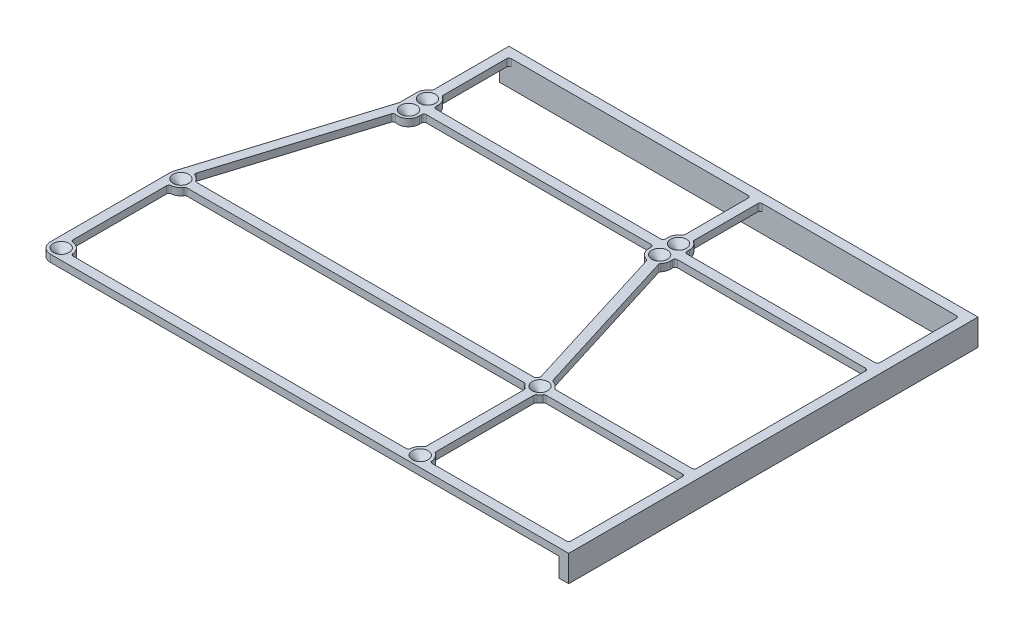
SolidWorks part; units mm, degrees
ref_plane "Front Plane" through (0, 0, 0) normal (0, 0, 1) x (1, 0, 0)
ref_plane "Top Plane" through (0, 0, 0) normal (0, 1, 0) x (1, 0, 0)
ref_plane "Right Plane" through (0, 0, 0) normal (1, 0, 0) x (0, 0, -1)
sketch "Sketch1" plane through (0, 0, 0) normal (0, 1, 0) x (1, 0, 0)
  line L0 (0, 0) -> (-83.045, 0)
  line L1 (-191.955, 0) -> (-191.955, 4)
  line L2 (-191.955, 4) -> (4, 4)
  line L3 (4, 4) -> (4, -167)
  line L4 (4, -167) -> (0, -167)
  line L5 (0, -163) -> (0, -114.5)
  line L6 (-189.955, -32.045) -> (-189.955, -39.955) construction
  line L7 (-245, -80) -> (-30, -80) construction
  line L8 (-245, -80) -> (-245, -195) construction
  line L9 (-245, -195) -> (-30, -195) construction
  line L10 (-30, -80) -> (-30, -195) construction
  line L11 (-212.5, -112.5) -> (-62.5, -112.5) construction
  line L12 (-212.5, -112.5) -> (-212.5, -162.5) construction
  line L13 (-212.5, -162.5) -> (-62.5, -162.5) construction
  line L14 (-62.5, -112.5) -> (-62.5, -162.5) construction
  line L15 (-193.55, -25) -> (-81.45, -25) construction
  line L16 (-193.55, -25) -> (-193.55, -47) construction
  line L17 (-193.55, -47) -> (-81.45, -47) construction
  line L18 (-81.45, -25) -> (-81.45, -47) construction
  line L19 (-189.955, -36) -> (-85.045, -36) construction
  line L20 (-85.045, -32.045) -> (-85.045, -39.955) construction
  line L21 (-194.455, -32.045) -> (-194.455, -39.2719)
  line L22 (-185.455, -32.045) -> (-185.455, -34)
  line L23 (-191.955, 0) -> (-191.955, -28.0139)
  line L24 (-187.955, -28.0139) -> (-187.955, 0)
  line L25 (-191.955, 0) -> (-187.955, 0) construction
  line L26 (-89.545, -32.045) -> (-89.545, -34)
  line L27 (-80.545, -32.045) -> (-80.545, -34)
  line L28 (-87.045, -28.0139) -> (-87.045, 0)
  line L29 (-83.045, -28.0139) -> (-83.045, 0)
  line L30 (-87.045, 0) -> (-187.955, 0)
  line L31 (-87.045, 0) -> (-83.045, 0) construction
  line L32 (-58.4689, -114.5) -> (0, -114.5)
  line L33 (-58.4689, -110.5) -> (0, -110.5)
  line L34 (-60.5, -116.5311) -> (-60.5, -158.4689)
  line L35 (0, -167) -> (-212.5, -167)
  line L36 (-58.0279, -163) -> (0, -163)
  line L37 (0, -163) -> (0, -167) construction
  line L38 (-208.0279, -163) -> (-66.9721, -163)
  line L39 (-64.5, -116.5311) -> (-64.5, -158.4689)
  line L40 (-213, -116.9721) -> (-213, -158.0279)
  line L41 (-208.4689, -114.5) -> (-66.5311, -114.5)
  line L42 (-216.7973, -111.1645) -> (-194.455, -39.2719)
  line L43 (-189.955, -39.955) -> (-212.5, -112.5) construction
  line L44 (-217, -112.5) -> (-217, -162.5)
  line L45 (-58.0279, -163) -> (-62.0031, -162.5556) construction
  line L46 (-191.7597, -44.0773) -> (-211.6503, -108.081)
  line L47 (-208.4689, -110.5) -> (-66.5311, -110.5)
  line L48 (-85.045, -39.955) -> (-62.5, -112.5) construction
  line L49 (-65.6062, -109.244) -> (-85.7586, -44.3981)
  line L50 (-61.7864, -108.0569) -> (-81.9388, -43.211)
  line L51 (-65.6062, -109.244) -> (-61.7864, -108.0569) construction
  line L52 (0, -110.5) -> (0, -38)
  line L53 (0, -110.5) -> (0, -114.5) construction
  line L54 (-64.5, -158.4689) -> (-60.5, -158.4689) construction
  line L55 (-213, -116.9721) -> (-217, -116.9721) construction
  line L56 (-66.5311, -110.5) -> (-66.5311, -114.5) construction
  line L57 (-211.6503, -108.081) -> (-215.4701, -106.8939) construction
  line L58 (-185.455, -34) -> (-89.545, -34)
  line L59 (-185.455, -38) -> (-89.545, -38)
  line L60 (-185.455, -38) -> (-185.455, -39.955)
  line L61 (-89.545, -38) -> (-89.545, -39.955)
  line L62 (-185.455, -34) -> (-185.455, -38) construction
  line L63 (-80.545, -34) -> (0, -34)
  line L64 (-80.545, -38) -> (0, -38)
  line L65 (-80.545, -38) -> (-80.545, -39.955)
  line L66 (0, -34) -> (0, 0)
  arc A0 (-66.9721, -163) -> (-64.5, -158.4689) centre (-62.5, -162.5) cw
  arc A1 (-60.5, -158.4689) -> (-58.0279, -163) centre (-62.5, -162.5) cw
  arc A2 (-212.5, -167) -> (-217, -162.5) centre (-212.5, -162.5) cw
  arc A3 (-213, -158.0279) -> (-208.0279, -163) centre (-212.5, -162.5) cw
  arc A4 (-185.455, -32.045) -> (-187.955, -28.0139) centre (-189.955, -32.045) ccw
  arc A5 (-191.7597, -44.0773) -> (-185.455, -39.955) centre (-189.955, -39.955) ccw
  arc A6 (-191.955, -28.0139) -> (-194.455, -32.045) centre (-189.955, -32.045) ccw
  arc A7 (-80.545, -32.045) -> (-83.045, -28.0139) centre (-85.045, -32.045) ccw
  arc A8 (-89.545, -39.955) -> (-85.7586, -44.3981) centre (-85.045, -39.955) ccw
  arc A9 (-87.045, -28.0139) -> (-89.545, -32.045) centre (-85.045, -32.045) ccw
  arc A10 (-58.4689, -110.5) -> (-61.7864, -108.0569) centre (-62.5, -112.5) ccw
  arc A11 (-58.4689, -114.5) -> (-60.5, -116.5311) centre (-62.5, -112.5) cw
  arc A12 (-208.4689, -114.5) -> (-213, -116.9721) centre (-212.5, -112.5) cw
  arc A13 (-66.5311, -114.5) -> (-64.5, -116.5311) centre (-62.5, -112.5) ccw
  arc A14 (-217, -112.5) -> (-216.7973, -111.1645) centre (-212.5, -112.5) cw
  circle A15 centre (-62.5, -162.5) radius 0.5
  circle A16 centre (-62.5, -112.5) radius 0.5
  circle A17 centre (-212.5, -112.5) radius 0.5
  circle A18 centre (-212.5, -162.5) radius 0.5
  arc A19 (-211.6503, -108.081) -> (-208.4689, -110.5) centre (-212.5, -112.5) cw
  arc A20 (-66.5311, -110.5) -> (-65.6062, -109.244) centre (-62.5, -112.5) cw
  arc A21 (-81.9388, -43.211) -> (-80.545, -39.955) centre (-85.045, -39.955) ccw
  circle A22 centre (-189.955, -32.045) radius 0.5
  circle A23 centre (-189.955, -39.955) radius 0.5
  circle A24 centre (-85.045, -32.045) radius 0.5
  circle A25 centre (-85.045, -39.955) radius 0.5
  point P25 (-137.5, -36)
  point P26 (-137.5, -25)
  point P27 (-81.45, -36)
  point P31 (-137.5, -80)
  dimension "D15" = 1
  dimension "D1" = 4
  dimension "D2" = 50
  dimension "D3" = 150
  dimension "D4" = 215
  dimension "D5" = 115
  dimension "D6" = 32.5
  dimension "D7" = 32.5
  dimension "D8" = 30
  dimension "D9" = 7.91
  dimension "D10" = 104.91
  dimension "D11" = 22
  dimension "D12" = 112.1
  dimension "D13" = 25
  dimension "D14" = 80
extrude "Boss-Extrude1" add sketch "Sketch1" along normal blind 3
sketch "Sketch2" plane through (0, 0, 0) normal (0, -1, 0) x (1, 0, 0)
  line L0 (4, -4) -> (4, 167)
  line L1 (4, 167) -> (0, 167)
  line L2 (-212.5, 167) -> (4, 167) construction
  line L3 (0, 167) -> (0, 0)
  line L4 (0, 0) -> (-191.955, 0)
  line L5 (-191.955, -4) -> (-191.955, 28.0139) construction
  line L6 (-191.955, 0) -> (-191.955, -4)
  line L7 (-191.955, -4) -> (4, -4)
extrude "Boss-Extrude2" add sketch "Sketch2" along normal blind 8
chamfer "Chamfer1" distance 2.8 angle 45 8 edges at (-212.5, 3, 163) (-212.5, 3, 113) (-62.5, 3, 163) (-62.5, 3, 113) (-85.045, 3, 40.455) (-85.045, 3, 32.545) (-189.955, 3, 40.455) (-189.955, 3, 32.545)
fillet "Fillet1" radius 1 41 edges at (-66.9721, 1.5, 163) (-64.5, 1.5, 158.4689) (-58.0279, 1.5, 163) (-60.5, 1.5, 158.4689) (0, 1.5, 163) (0, 1.5, 114.5) (-64.5, 1.5, 116.5311) (-66.5311, 1.5, 114.5) (-60.5, 1.5, 116.5311) (-58.4689, 1.5, 114.5) (-58.4689, 1.5, 110.5) (-61.7864, 1.5, 108.0569) (-66.5311, 1.5, 110.5) (-65.6062, 1.5, 109.244) (0, 1.5, 110.5) (0, 1.5, 34) (-87.045, 1.5, 28.0139) (-81.9388, 1.5, 43.211) (0, 1.5, 38) (0, -2.5, 0) (-83.045, 1.5, 0) (-83.045, 1.5, 28.0139) (-80.545, 1.5, 34) (-80.545, 1.5, 38) (-85.7586, 1.5, 44.3981) (-89.545, 1.5, 38) (-87.045, 1.5, 0) (-89.545, 1.5, 34) (-187.955, 1.5, 0) (-194.455, 1.5, 39.2719) (-191.955, 1.5, 28.0139) (-187.955, 1.5, 28.0139) (-185.455, 1.5, 34) (-191.7597, 1.5, 44.0773) (-185.455, 1.5, 38) (-208.4689, 1.5, 110.5) (-211.6503, 1.5, 108.081) (-213, 1.5, 116.9721) (-208.4689, 1.5, 114.5) (-208.0279, 1.5, 163) (-213, 1.5, 158.0279)
